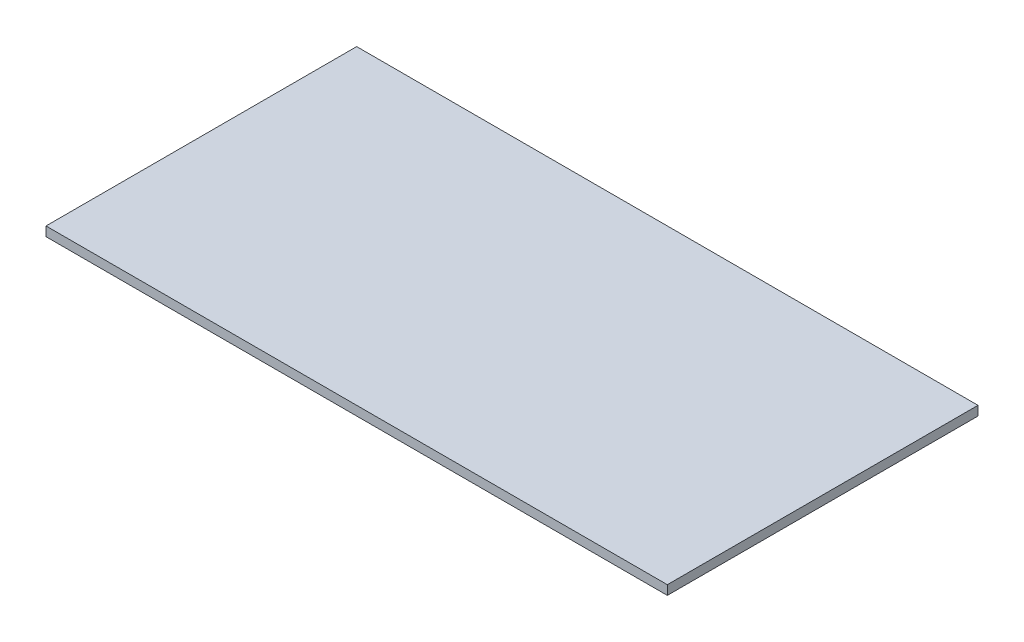
SolidWorks part; units mm, degrees
material "Cedar"
ref_plane "Front Plane" through (0, 0, 0) normal (0, 0, 1) x (1, 0, 0)
ref_plane "Top Plane" through (0, 0, 0) normal (0, 1, 0) x (1, 0, 0)
ref_plane "Right Plane" through (0, 0, 0) normal (1, 0, 0) x (0, 0, -1)
sketch "Sketch1" plane through (0, 0, 0) normal (0, 1, 0) x (1, 0, 0)
  line L1 (-609.6, -304.8) -> (609.6, -304.8)
  line L2 (-609.6, -304.8) -> (-609.6, 304.8)
  line L3 (-609.6, 304.8) -> (609.6, 304.8)
  line L4 (609.6, -304.8) -> (609.6, 304.8)
  line L5 (-609.6, -304.8) -> (609.6, 304.8) construction
  line L6 (-609.6, 304.8) -> (609.6, -304.8) construction
  point P0 (0, 0)
  dimension "D1" = 1219.2
  dimension "D2" = 609.6
extrude "Boss-Extrude1" add sketch "Sketch1" along normal blind 18.2562
